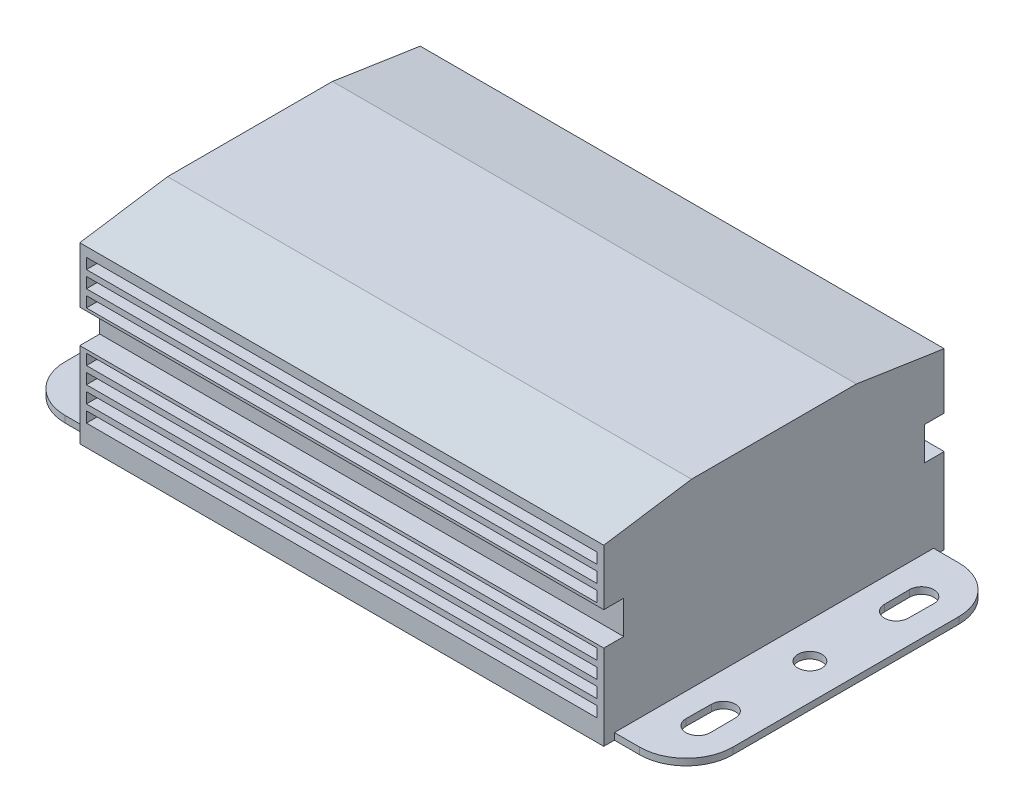
SolidWorks part; units mm, degrees
ref_plane "Front Plane" through (0, 0, 0) normal (0, 0, 1) x (1, 0, 0)
ref_plane "Top Plane" through (0, 0, 0) normal (0, 1, 0) x (1, 0, 0)
ref_plane "Right Plane" through (0, 0, 0) normal (1, 0, 0) x (0, 0, -1)
sketch "Sketch1" plane through (0, 0, 0) normal (0, 1, 0) x (1, 0, 0)
  line L0 (0, 33.528) -> (-127.508, 33.528) construction
  line L1 (0, 0) -> (-127.508, 0) construction
  line L2 (0, 11.938) -> (0, 55.118)
  line L3 (-13.716, 66.04) -> (-113.792, 66.04)
  line L4 (-127.508, 11.938) -> (-127.508, 55.118)
  line L5 (-63.754, 0) -> (-63.754, 66.04) construction
  line L6 (-113.792, 66.04) -> (-113.792, 64.008)
  line L7 (-113.792, 64.008) -> (-118.618, 64.008)
  line L8 (-113.792, 3.048) -> (-118.618, 3.048)
  line L9 (-113.792, 1.016) -> (-113.792, 3.048)
  line L10 (-13.716, 66.04) -> (-13.716, 64.008)
  line L11 (-13.716, 64.008) -> (-8.89, 64.008)
  line L12 (-13.716, 3.048) -> (-8.89, 3.048)
  line L13 (-13.716, 1.016) -> (-13.716, 3.048)
  line L14 (-113.792, 1.016) -> (-13.716, 1.016)
  line L15 (-113.792, 64.008) -> (-113.792, 3.048) construction
  line L16 (-118.3677, 17.018) -> (-118.3253, 12.192)
  line L17 (-122.9747, 12.192) -> (-122.9323, 17.018)
  line L18 (-122.9747, 54.864) -> (-122.9323, 50.038)
  line L19 (-118.3677, 50.038) -> (-118.3253, 54.864)
  line L20 (-120.65, 31.242) -> (-120.65, 19.3003) construction
  line L21 (-9.1403, 50.038) -> (-9.1827, 54.864)
  line L22 (-4.5333, 54.864) -> (-4.5757, 50.038)
  line L23 (-4.5333, 12.192) -> (-4.5757, 17.018)
  line L24 (-9.1403, 17.018) -> (-9.1827, 12.192)
  arc A0 (-118.618, 3.048) -> (-127.508, 11.938) centre (-118.618, 11.938) cw
  arc A1 (-118.618, 64.008) -> (-127.508, 55.118) centre (-118.618, 55.118) ccw
  arc A2 (-8.89, 3.048) -> (0, 11.938) centre (-8.89, 11.938) ccw
  arc A3 (-8.89, 64.008) -> (0, 55.118) centre (-8.89, 55.118) cw
  circle A4 centre (-120.65, 33.528) radius 2.286
  arc A5 (-118.3677, 17.018) -> (-122.9323, 17.018) centre (-120.65, 17.018) ccw
  arc A6 (-122.9747, 12.192) -> (-118.3253, 12.192) centre (-120.65, 12.192) ccw
  arc A7 (-122.9747, 54.864) -> (-118.3253, 54.864) centre (-120.65, 54.864) cw
  arc A8 (-118.3677, 50.038) -> (-122.9323, 50.038) centre (-120.65, 50.038) cw
  arc A9 (-9.1403, 50.038) -> (-4.5757, 50.038) centre (-6.858, 50.038) ccw
  arc A10 (-4.5333, 54.864) -> (-9.1827, 54.864) centre (-6.858, 54.864) ccw
  arc A11 (-4.5333, 12.192) -> (-9.1827, 12.192) centre (-6.858, 12.192) cw
  arc A12 (-9.1403, 17.018) -> (-4.5757, 17.018) centre (-6.858, 17.018) cw
  circle A13 centre (-6.858, 33.528) radius 2.286
  point P21 (-127.508, 3.048)
  point P24 (-127.508, 64.008)
  dimension "D1" = 8.89
  dimension "D3" = 4.572
  dimension "D2" = 127.508
  dimension "D4" = 13.716
  dimension "D5" = 6.858
  dimension "D6" = 16.51
  dimension "D7" = 21.336
  dimension "D8" = 60.96
extrude "Boss-Extrude1" add sketch "Sketch1" along normal blind 35.814
sketch "Sketch3" plane through (0, 35.814, 0) normal (0, 1, 0) x (1, 0, 0)
  line L1 (-13.716, 64.008) -> (0, 64.008)
  line L2 (-13.716, 64.008) -> (-13.716, 3.048)
  line L3 (-13.716, 3.048) -> (0, 3.048)
  line L4 (0, 64.008) -> (0, 3.048)
  line L5 (-113.792, 3.048) -> (-127.508, 3.048)
  line L6 (-113.792, 3.048) -> (-113.792, 64.008)
  line L7 (-113.792, 64.008) -> (-127.508, 64.008)
  line L8 (-127.508, 3.048) -> (-127.508, 64.008)
extrude "Cut-Extrude2" cut sketch "Sketch3" against normal blind 34.544
sketch "Sketch4" plane through (-113.792, 0, 0) normal (-1, 0, 0) x (0, 0, 1)
  line L0 (-17.78, 35.814) -> (-1.016, 33.274)
  line L1 (-1.016, 35.814) -> (-66.04, 35.814) construction
  line L2 (-1.016, 35.814) -> (-1.016, 0) construction
  line L3 (-1.016, 33.274) -> (-1.016, 35.814)
  line L4 (-1.016, 35.814) -> (-17.78, 35.814)
  line L5 (-33.528, 35.814) -> (-33.528, -10.102) construction
  line L6 (-66.04, 22.606) -> (-66.04, 16.256)
  line L7 (-1.016, 22.606) -> (-4.826, 22.606)
  line L8 (-1.016, 22.606) -> (-1.016, 16.256)
  line L9 (-1.016, 16.256) -> (-4.826, 16.256)
  line L10 (-4.826, 22.606) -> (-4.826, 16.256)
  line L11 (-66.04, 16.256) -> (-62.23, 16.256)
  line L12 (-62.23, 22.606) -> (-62.23, 16.256)
  line L13 (-66.04, 22.606) -> (-62.23, 22.606)
  line L14 (-66.04, 33.274) -> (-66.04, 35.814)
  line L15 (-49.276, 35.814) -> (-66.04, 33.274)
  line L16 (-66.04, 35.814) -> (-49.276, 35.814)
  dimension "D1" = 16.764
  dimension "D2" = 2.54
  dimension "D3" = 10.668
  dimension "D4" = 6.35
  dimension "D5" = 3.81
extrude "Cut-Extrude3" cut sketch "Sketch4" against normal through all
sketch "Sketch5" plane through (0, 0, -1.016) normal (0, 0, 1) x (1, 0, 0)
  line L1 (-112.522, 29.464) -> (-14.986, 29.464)
  line L2 (-112.522, 29.464) -> (-112.522, 31.496)
  line L3 (-112.522, 31.496) -> (-14.986, 31.496)
  line L4 (-14.986, 29.464) -> (-14.986, 31.496)
  line L5 (-113.792, 33.274) -> (-113.792, 22.606) construction
  line L6 (-13.716, 33.274) -> (-13.716, 22.606) construction
  line L7 (-109.982, 29.464) -> (-14.986, 29.464)
  line L9 (-109.982, 31.496) -> (-14.986, 31.496)
  line L27 (-109.982, 29.464) -> (-109.982, 31.496) [skipped]
  line L28 (-109.982, 26.416) -> (-109.982, 28.448) [skipped]
  line L29 (-109.982, 23.368) -> (-109.982, 25.4) [skipped]
  line L30 (-12.446, 23.368) -> (-12.446, 25.4) [skipped]
  line L31 (-12.446, 29.464) -> (-12.446, 31.496) [skipped]
  line L32 (-12.446, 26.416) -> (-12.446, 28.448) [skipped]
  line L53 (-112.522, 26.416) -> (-14.986, 26.416) [skipped]
  line L54 (-112.522, 26.416) -> (-112.522, 28.448) [skipped]
  line L55 (-112.522, 28.448) -> (-14.986, 28.448) [skipped]
  line L56 (-14.986, 26.416) -> (-14.986, 28.448) [skipped]
  line L57 (-109.982, 26.416) -> (-14.986, 26.416) [skipped]
  line L58 (-109.982, 28.448) -> (-14.986, 28.448) [skipped]
  line L59 (-112.522, 23.368) -> (-14.986, 23.368) [skipped]
  line L60 (-112.522, 23.368) -> (-112.522, 25.4) [skipped]
  line L61 (-112.522, 25.4) -> (-14.986, 25.4) [skipped]
  line L62 (-14.986, 23.368) -> (-14.986, 25.4) [skipped]
  line L63 (-109.982, 23.368) -> (-14.986, 23.368) [skipped]
  line L64 (-109.982, 25.4) -> (-14.986, 25.4) [skipped]
  dimension "D3" = 1.27
  dimension "D4" = 1.27
  dimension "D5" = 2
  dimension "D6" = 3
extrude "Cut-Extrude6" cut sketch "Sketch5" against normal blind 3.048 contours L1 L4 L3 L2
pattern_linear "LPattern1" count 9 spacing 3.175 along (0, -1, 0) skipping (3, 0), (4, 0) of "Cut-Extrude6"
ref_plane "Plane1" through (0, 0, -33.528) normal (0, 0, 1) x (1, 0, 0)
mirror "Mirror1" about plane through (0, 0, -33.528) normal (0, 0, 1) of "LPattern1", "Cut-Extrude6"
